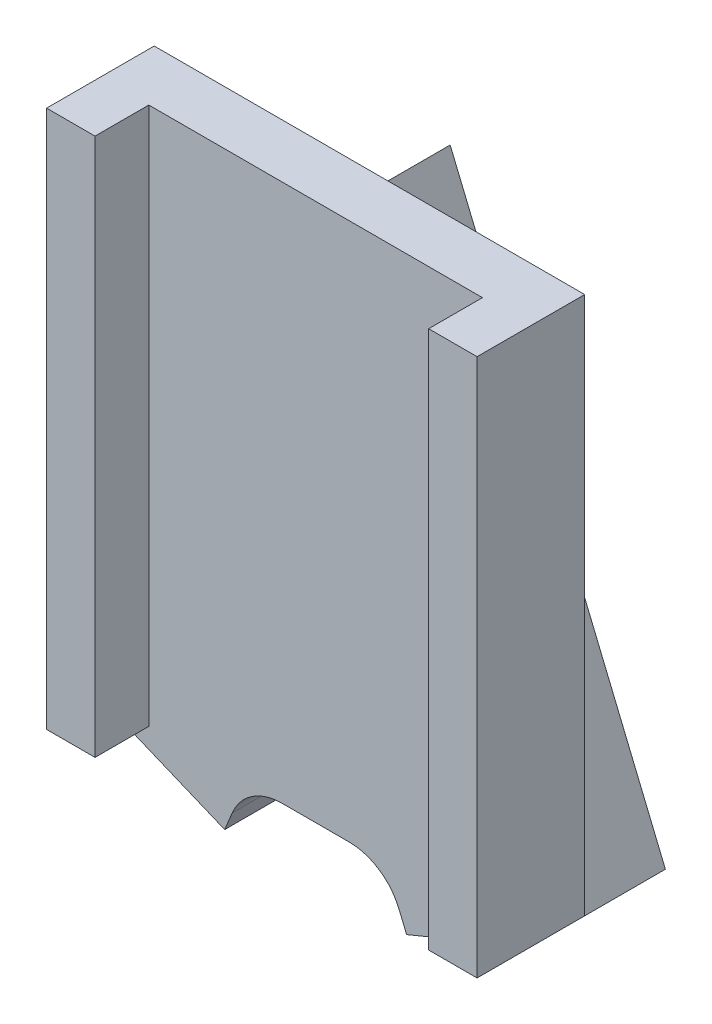
SolidWorks part; units mm, degrees
material "PA Type 6"
ref_plane "Ebene vorne" through (0, 0, 0) normal (0, 0, 1) x (1, 0, 0)
ref_plane "Ebene oben" through (0, 0, 0) normal (0, 1, 0) x (1, 0, 0)
ref_plane "Ebene rechts" through (0, 0, 0) normal (1, 0, 0) x (0, 0, -1)
sketch "Sketch1" plane through (0, 0, 0) normal (0, 0, 1) x (1, 0, 0)
  line L1 (0, 0) -> (8, 0)
  line L2 (0, 0) -> (0, -10)
  line L3 (0, -10) -> (8, -10)
  line L4 (8, 0) -> (8, -10)
extrude "Boss-Extrude1" add sketch "Sketch1" along normal blind 2
sketch "Sketch2" plane through (0, 0, 2) normal (0, 0, 1) x (1, 0, 0)
  line L0 (8, 0) -> (0, 0) construction
  line L1 (0.9, 0) -> (7.1, 0)
  line L2 (0.9, 0) -> (0.9, -10)
  line L3 (0.9, -10) -> (7.1, -10)
  line L4 (7.1, 0) -> (7.1, -10)
  line L5 (0, -10) -> (8, -10) construction
  line L6 (0, 0) -> (0, -10) construction
  line L7 (8, -10) -> (8, 0) construction
  dimension "D1" = 0.9
  dimension "D2" = 0.9
  dimension "D3" = 6.2
extrude "Cut-Extrude1" cut sketch "Sketch2" against normal blind 1
sketch "Sketch3" plane through (0, 0, 0) normal (0, 0, -1) x (-1, 0, 0)
  line L0 (-8, -10) -> (-4, -0.3431)
  line L1 (-8, -10) -> (-5.6903, -10.9567)
  line L4 (-4, 0) -> (-4, -10) construction
  line L5 (-8, 0) -> (0, 0) construction
  line L6 (0, -10) -> (-8, -10) construction
  line L7 (-8, -5) -> (0, -5) construction
  line L8 (-8, -10) -> (-8, 0) construction
  line L9 (0, 0) -> (0, -10) construction
  line L10 (0, -10) -> (-4, -0.3431)
  line L11 (-4, -6.876) -> (-5.6903, -10.9567)
  line L12 (0, -10) -> (-2.3097, -10.9567)
  line L13 (-2.3097, -10.9567) -> (-4, -6.876)
  dimension "D1" = 2.5
  dimension "D2" = 2.5
  dimension "D3" = 45
extrude "Boss-Extrude2" add sketch "Sketch3" along normal blind 1.5 and the other way blind 1
hole_wizard "M1 Clearance Hole2" positions "Sketch5" profile "Sketch4" hole size "M1" standard "DIN"
sketch "Sketch5" plane through (-3.5355, -8.5355, 0) normal (-0.3827, -0.9239, 0) x (-0.9239, 0.3827, 0)
  line L0 (-5.0768, 1.5) -> (-5.0768, -1) construction
  line L1 (-6.3268, 1.5) -> (-3.8268, 1.5) construction
  line L2 (-6.3268, -1) -> (-3.8268, -1) construction
  line L4 (-6.3268, 0.25) -> (-3.8268, 0.25) construction
  line L5 (-6.3268, -1) -> (-6.3268, 1.5) construction
  line L6 (-3.8268, 0) -> (-3.8268, 1.5) construction
  point P0 (-5.116, 0.25)
sketch "Sketch4" plane through (1.191, -10.4933, -0.25) normal (0, 0, 1) x (0.9239, -0.3827, 0)
  line L0 (0, 0) -> (0, 5.3605)
  line L1 (0, 5.3605) -> (0.6, 5)
  line L2 (0.6, 5) -> (0.6, 0)
  line L5 (0.6, 0) -> (0, 0)
  line L10 (0, 5.3605) -> (-0.6, 5) construction
  line L11 (0, -6.35) -> (0, 107.95) construction
  dimension "Hole Dia." = 1.2
  dimension "Hole Depth" = 5
  dimension "Drill Angle" = 118
hole_wizard "M1 Clearance Hole1" positions "Sketch6" profile "Sketch7" hole size "M1" standard "DIN"
sketch "Sketch6" plane through (4.7071, -11.364, 0) normal (0.3827, -0.9239, 0) x (-0.9239, -0.3827, 0)
  point P0 (-2.3142, 0.25)
  point P18 (0, 0)
sketch "Sketch7" plane through (6.8452, -10.4784, -0.25) normal (0, 0, 1) x (0.9239, 0.3827, 0)
  line L0 (0, 0) -> (0, 5.3004)
  line L1 (0, 5.3004) -> (0.5, 5)
  line L2 (0.5, 5) -> (0.5, 0)
  line L5 (0.5, 0) -> (0, 0)
  line L10 (0, 5.3004) -> (-0.5, 5) construction
  line L11 (0, -6.35) -> (0, 107.95) construction
  dimension "Hole Dia." = 1
  dimension "Hole Depth" = 5
  dimension "Drill Angle" = 118
sketch "Sketch8" plane through (0, 0, -1.5) normal (0, 0, -1) x (-1, 0, 0)
  circle A0 centre (-4, -7.3) radius 0.4
extrude "Cut-Extrude2" cut sketch "Sketch8" against normal blind 1.5
fillet "Fillet2" radius 1 2 edges at (2.706, -10, 0.5) (5.294, -10, 0.5)
